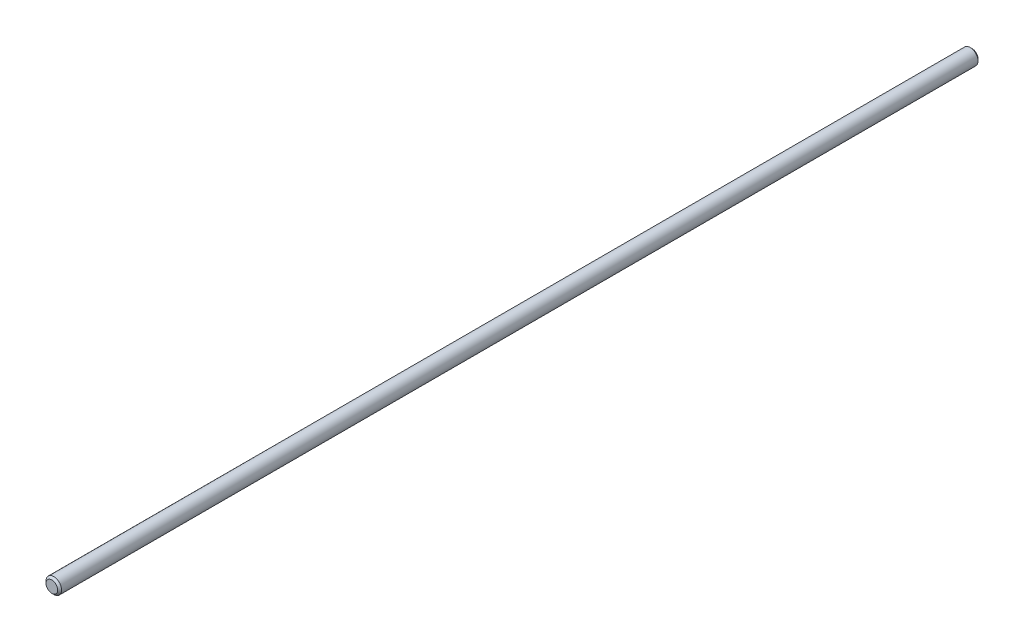
SolidWorks part; units mm, degrees
ref_plane "Front Plane" through (0, 0, 0) normal (0, 0, 1) x (1, 0, 0)
ref_plane "Top Plane" through (0, 0, 0) normal (0, 1, 0) x (1, 0, 0)
ref_plane "Right Plane" through (0, 0, 0) normal (1, 0, 0) x (0, 0, -1)
sketch "Sketch1" plane through (0, 0, 0) normal (0, 0, 1) x (1, 0, 0)
  circle A0 centre (0, 0) radius 3.975
  dimension "D1" = 7.95
extrude "Boss-Extrude1" add sketch "Sketch1" along normal blind 470
chamfer "Chamfer1" distance 1 angle 45 2 edges at (3.975, 0, 0) (3.975, 0, 470)
